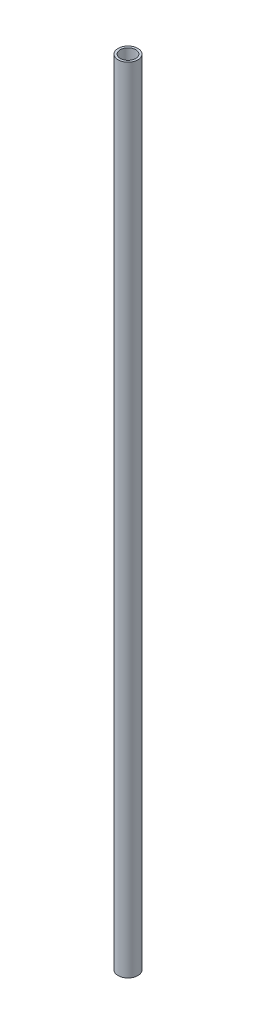
SolidWorks part; units mm, degrees
ref_plane "Front Plane" through (0, 0, 0) normal (0, 0, 1) x (1, 0, 0)
ref_plane "Top Plane" through (0, 0, 0) normal (0, 1, 0) x (1, 0, 0)
ref_plane "Right Plane" through (0, 0, 0) normal (1, 0, 0) x (0, 0, -1)
sketch "Sketch1" plane through (0, 0, 0) normal (0, 1, 0) x (1, 0, 0)
  circle A0 centre (0, 0) radius 1.5875
  dimension "D1" = 3.175
extrude "Boss-Extrude1" add sketch "Sketch1" along normal blind 127
sketch "Sketch2" plane through (0, 127, 0) normal (0, 1, 0) x (1, 0, 0)
  circle A0 centre (0, 0) radius 1.2319
  dimension "D1" = 2.4638
extrude "Cut-Extrude1" cut sketch "Sketch2" against normal through all
